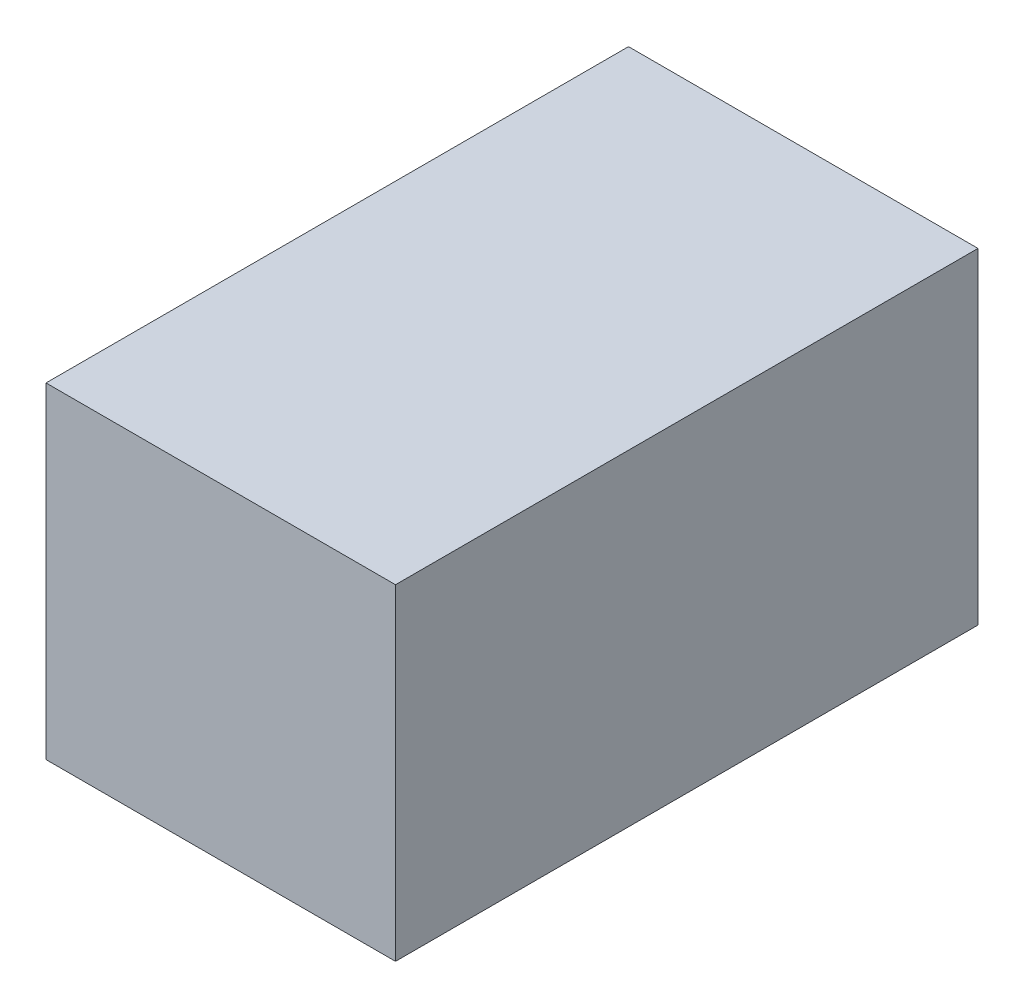
SolidWorks part; units mm, degrees
ref_plane "Front Plane" through (0, 0, 0) normal (0, 0, 1) x (1, 0, 0)
ref_plane "Top Plane" through (0, 0, 0) normal (0, 1, 0) x (1, 0, 0)
ref_plane "Right Plane" through (0, 0, 0) normal (1, 0, 0) x (0, 0, -1)
sketch "Sketch1" plane through (0, 0, 0) normal (0, 0, 1) x (1, 0, 0)
  line L0 (0, 0) -> (3, 0)
  line L1 (3, -2.8) -> (0, -2.8)
  line L2 (0, -2.8) -> (0, 0)
  line L3 (3, 0) -> (3, -2.8)
  dimension "D1" = 2.8
  dimension "D2" = 3
extrude "Boss-Extrude1" add sketch "Sketch1" along normal blind 5
